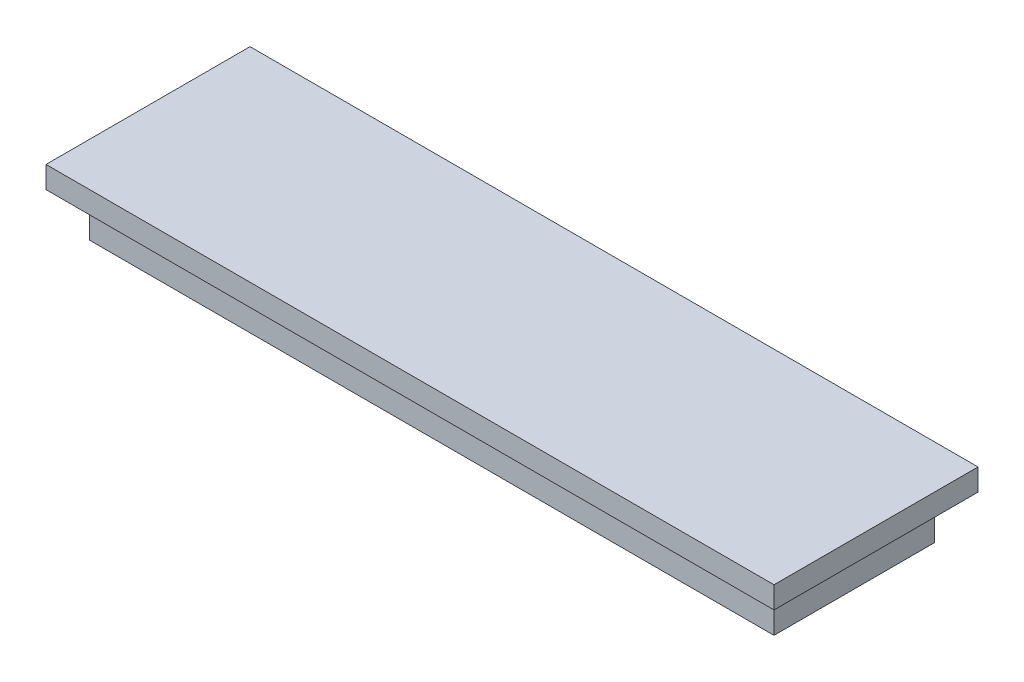
SolidWorks part; units mm, degrees
ref_plane "Front Plane" through (0, 0, 0) normal (0, 0, 1) x (1, 0, 0)
ref_plane "Top Plane" through (0, 0, 0) normal (0, 1, 0) x (1, 0, 0)
ref_plane "Right Plane" through (0, 0, 0) normal (1, 0, 0) x (0, 0, -1)
sketch "Sketch1" plane through (0, 0, 0) normal (0, 1, 0) x (1, 0, 0)
  line L0 (-24.892, 5.842) -> (-24.892, -5.842)
  line L1 (-25.4, 6.35) -> (25.4, 6.35) construction
  line L2 (-25.4, 6.35) -> (-25.4, -6.35) construction
  line L3 (-25.4, -6.35) -> (25.4, -6.35) construction
  line L4 (25.4, 6.35) -> (25.4, -6.35) construction
  line L5 (-25.4, 6.35) -> (25.4, -6.35) construction
  line L6 (-25.4, -6.35) -> (25.4, 6.35) construction
  line L7 (-24.892, -5.842) -> (24.892, -5.842)
  line L8 (24.892, 5.842) -> (24.892, -5.842)
  line L9 (-24.892, 5.842) -> (24.892, 5.842)
  point P0 (0, 0)
  dimension "D1" = 50.8
  dimension "D2" = 12.7
  dimension "D3" = 0.508
extrude "Boss-Extrude1" add sketch "Sketch1" along normal blind 3.175
sketch "Sketch2" plane through (0, 3.175, 0) normal (0, 1, 0) x (1, 0, 0)
  line L8 (26.4668, 7.4168) -> (-26.4668, 7.4168)
  line L9 (-26.4668, 7.4168) -> (-26.4668, -7.4168)
  line L10 (-26.4668, -7.4168) -> (26.4668, -7.4168)
  line L11 (26.4668, -7.4168) -> (26.4668, 7.4168)
  line L12 (26.4668, 7.4168) -> (-26.4668, 7.4168)
  line L13 (-26.4668, 7.4168) -> (-26.4668, -7.4168)
  line L14 (-26.4668, -7.4168) -> (26.4668, -7.4168)
  line L15 (26.4668, -7.4168) -> (26.4668, 7.4168)
  dimension "D1" = 1.5748
extrude "Boss-Extrude2" add sketch "Sketch2" along normal blind 1.5875
